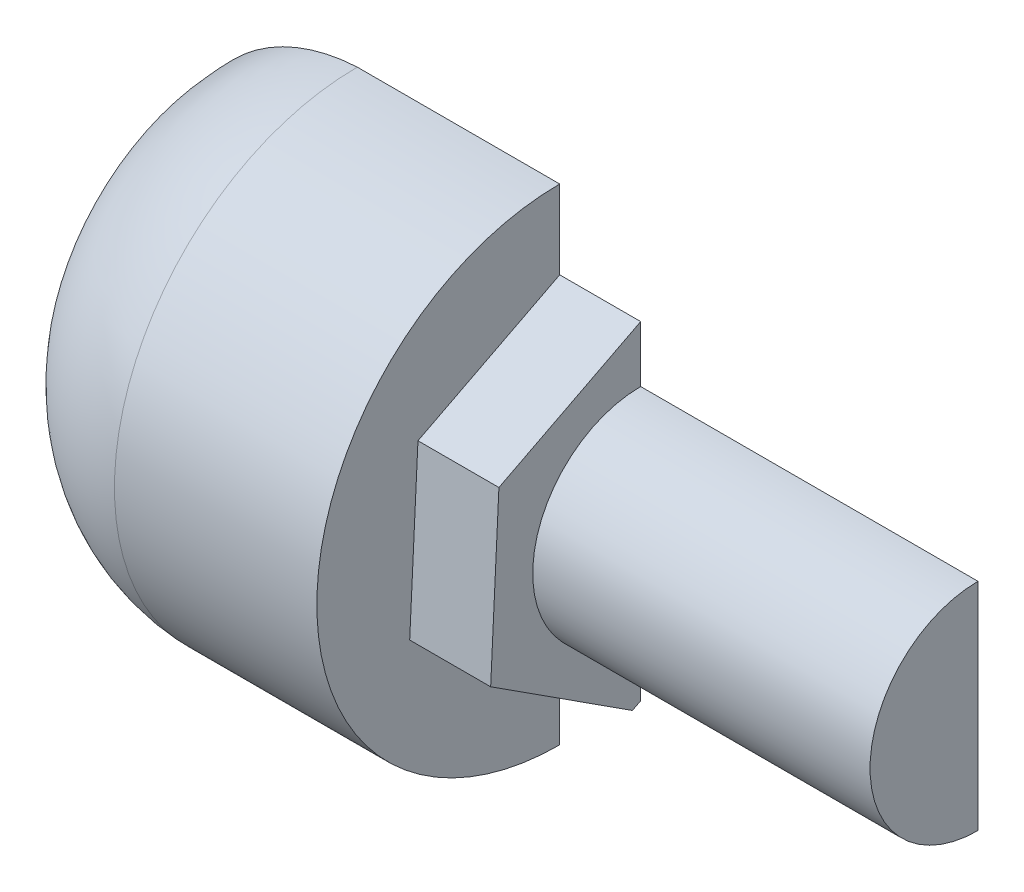
SolidWorks part; units mm, degrees
material "AISI 321 Tavlı Paslanmaz Çelik (SS)"
ref_plane "Ön Düzlem" through (0, 0, 0) normal (0, 0, 1) x (1, 0, 0)
ref_plane "Üst Düzlem" through (0, 0, 0) normal (0, 1, 0) x (1, 0, 0)
ref_plane "Sağ Düzlem" through (0, 0, 0) normal (1, 0, 0) x (0, 0, -1)
sketch "Çizim1" plane through (0, 0, 0) normal (0, 0, 1) x (1, 0, 0)
  line L0 (-25, 13) -> (-23.9, 11.25)
  line L3 (-23.9, 11.25) -> (-21.9133, 10.75)
  line L6 (-0.1535, 1.75) -> (-0.1535, 0)
  line L7 (0, 18) -> (0, 0)
  line L8 (0, 18) -> (-15, 18)
  line L9 (-0.1535, 0) -> (0, 0)
  arc A0 (-15, 18) -> (-25, 13) centre (-14.3013, 4.1026) ccw
  arc A3 (-0.1535, 1.75) -> (-21.9133, 10.75) centre (-13.8905, -0.6577) ccw
revolve "Döndür1" add sketch "Çizim1" angle 360 about L9
sketch "Çizim2" plane through (0, 0, 0) normal (1, 0, 0) x (0, 0, -1)
  line L1 (-0.6134, -12.4846) -> (10.5053, -6.7735)
  line L2 (10.5053, -6.7735) -> (11.1186, 5.7111)
  line L3 (11.1186, 5.7111) -> (0.6134, 12.4846)
  line L4 (0.6134, 12.4846) -> (-10.5053, 6.7735)
  line L5 (-10.5053, 6.7735) -> (-11.1186, -5.7111)
  line L6 (-11.1186, -5.7111) -> (-0.6134, -12.4846)
  circle A0 centre (0, 0) radius 10.825 construction
extrude "Yükseklik-Ekstrüzyon1" add sketch "Çizim2" along normal blind 6
sketch "Çizim3" plane through (6, 0, 0) normal (1, 0, 0) x (0, 0, -1)
  circle A0 centre (0, 0) radius 8
extrude "Boss-Extrude1" add sketch "Çizim3" along normal blind 25
sketch "Sketch3" plane through (31, 0, 0) normal (1, 0, 0) x (0, 0, -1)
  line L0 (0, 0) -> (0, -8)
  line L1 (0, -8) -> (0, 8)
  line L4 (0, -8) -> (0, -37.6597)
  line L5 (0, -37.6597) -> (31.5528, -37.6597)
  line L6 (31.5528, -8) -> (31.5528, -37.6597)
  line L7 (31.5528, -37.6597) -> (0, -37.6597)
  line L8 (31.5528, -37.6597) -> (31.5528, 22.8223)
  line L9 (31.5528, 22.8223) -> (0, 22.8223)
  line L10 (0, -37.6597) -> (0, 22.8223)
  circle A0 centre (0, 0) radius 8 construction
  circle M1 centre (0, 0) radius 8
extrude "Cut-Extrude2" cut sketch "Sketch3" against normal blind 67 contours L10 L4 L5 L6 L8 L9 M1 | L1 L0 M1
